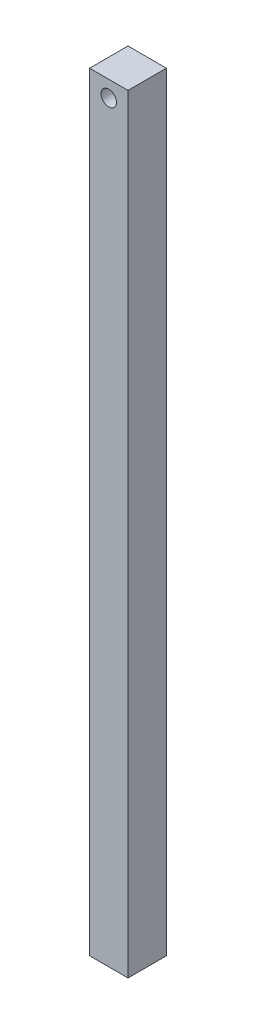
SolidWorks part; units mm, degrees
ref_plane "Front Plane" through (0, 0, 0) normal (0, 0, 1) x (1, 0, 0)
ref_plane "Top Plane" through (0, 0, 0) normal (0, 1, 0) x (1, 0, 0)
ref_plane "Right Plane" through (0, 0, 0) normal (1, 0, 0) x (0, 0, -1)
sketch "Sketch1" plane through (0, 0, 0) normal (0, 0, 1) x (1, 0, 0)
  line L1 (-2.5, 50) -> (2.5, 50)
  line L2 (-2.5, 50) -> (-2.5, -50)
  line L3 (-2.5, -50) -> (2.5, -50)
  line L4 (2.5, 50) -> (2.5, -50)
  line L5 (-2.5, 50) -> (2.5, -50) construction
  line L6 (-2.5, -50) -> (2.5, 50) construction
  point P0 (0, 0)
  dimension "D1" = 5
  dimension "D2" = 100
extrude "Boss-Extrude1" add sketch "Sketch1" along normal blind 5
sketch "Sketch3" plane through (0, 0, 5) normal (0, 0, 1) x (1, 0, 0)
  circle A0 centre (0, 47.885) radius 1
extrude "Cut-Extrude2" cut sketch "Sketch3" against normal through all
